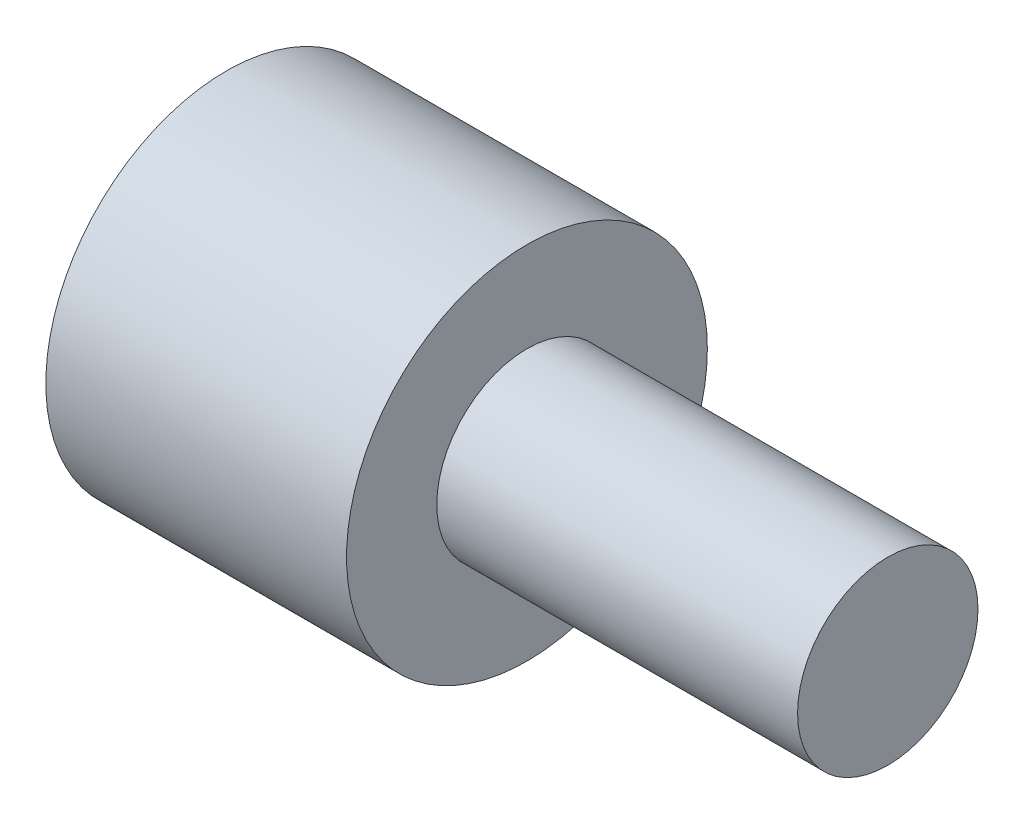
SolidWorks part; units mm, degrees
ref_plane "Ebene vorne" through (0, 0, 0) normal (0, 0, 1) x (1, 0, 0)
ref_plane "Ebene oben" through (0, 0, 0) normal (0, 1, 0) x (1, 0, 0)
ref_plane "Ebene rechts" through (0, 0, 0) normal (1, 0, 0) x (0, 0, -1)
sketch "Skizze1" plane through (0, 0, 0) normal (0, 0, 1) x (1, 0, 0)
  line L0 (0, 3) -> (5, 3)
  line L1 (5, 3) -> (5, 1.5)
  line L2 (5, 1.5) -> (11, 1.5)
  line L3 (11, 1.5) -> (11, 0)
  line L4 (11, 0) -> (0, 0)
  line L5 (0, 0) -> (0, 3)
  dimension "D1" = 5
  dimension "D2" = 6
  dimension "D3" = 3
  dimension "D4" = 1.5
revolve "Rotation1" add sketch "Skizze1" angle 360 about L4
cosmetic thread "Gewindedarstellung1" parameters "D2"=2.439
hole_wizard "M3 Gewindebohrung1" positions "Skizze3" profile "Skizze2" tap size "M3" standard "DIN"
sketch "Skizze3" plane through (0, 0, 0) normal (-1, 0, 0) x (0, 0, 1)
  point P0 (0, 0)
sketch "Skizze2" plane through (0, 0, 0) normal (0, 1, 0) x (0, 0, 1)
  line L0 (0, 0) -> (0, 5.7511)
  line L1 (0, 5.7511) -> (1.25, 5)
  line L2 (1.25, 5) -> (1.25, 0)
  line L5 (1.25, 0) -> (0, 0)
  line L10 (0, 5.7511) -> (-1.25, 5) construction
  line L11 (0, -6.35) -> (0, 107.95) construction
  dimension "Bohrerdurchmesser" = 2.5
  dimension "Bohrungstiefe" = 5
  dimension "Spitzenwinkel" = 118
cosmetic thread "Bohrungsgewinde1"
